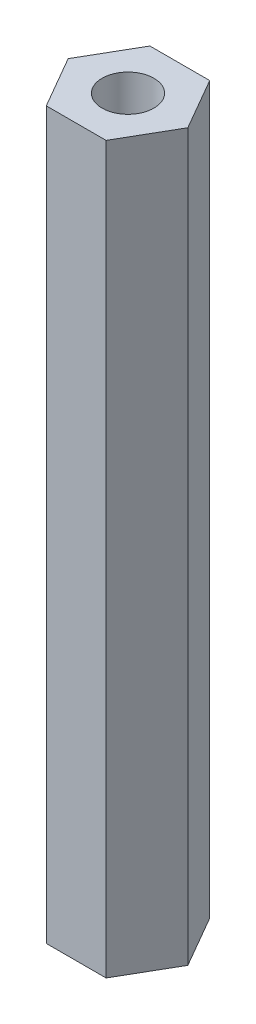
SolidWorks part; units mm, degrees
ref_plane "Front Plane" through (0, 0, 0) normal (0, 0, 1) x (1, 0, 0)
ref_plane "Top Plane" through (0, 0, 0) normal (0, 1, 0) x (1, 0, 0)
ref_plane "Right Plane" through (0, 0, 0) normal (1, 0, 0) x (0, 0, -1)
sketch "Sketch1" plane through (0, 0, 0) normal (0, 1, 0) x (1, 0, 0)
  line L1 (1.7321, 3) -> (-1.7321, 3)
  line L2 (-1.7321, 3) -> (-3.4641, 0)
  line L3 (-3.4641, 0) -> (-1.7321, -3)
  line L4 (-1.7321, -3) -> (1.7321, -3)
  line L5 (1.7321, -3) -> (3.4641, 0)
  line L6 (3.4641, 0) -> (1.7321, 3)
  circle A0 centre (0, 0) radius 3 construction
  circle A1 centre (0, 0) radius 1.5
  dimension "D3" = 3
  dimension "D1" = 6
  dimension "D2" = 6
extrude "Boss-Extrude1" add sketch "Sketch1" along normal blind 42
